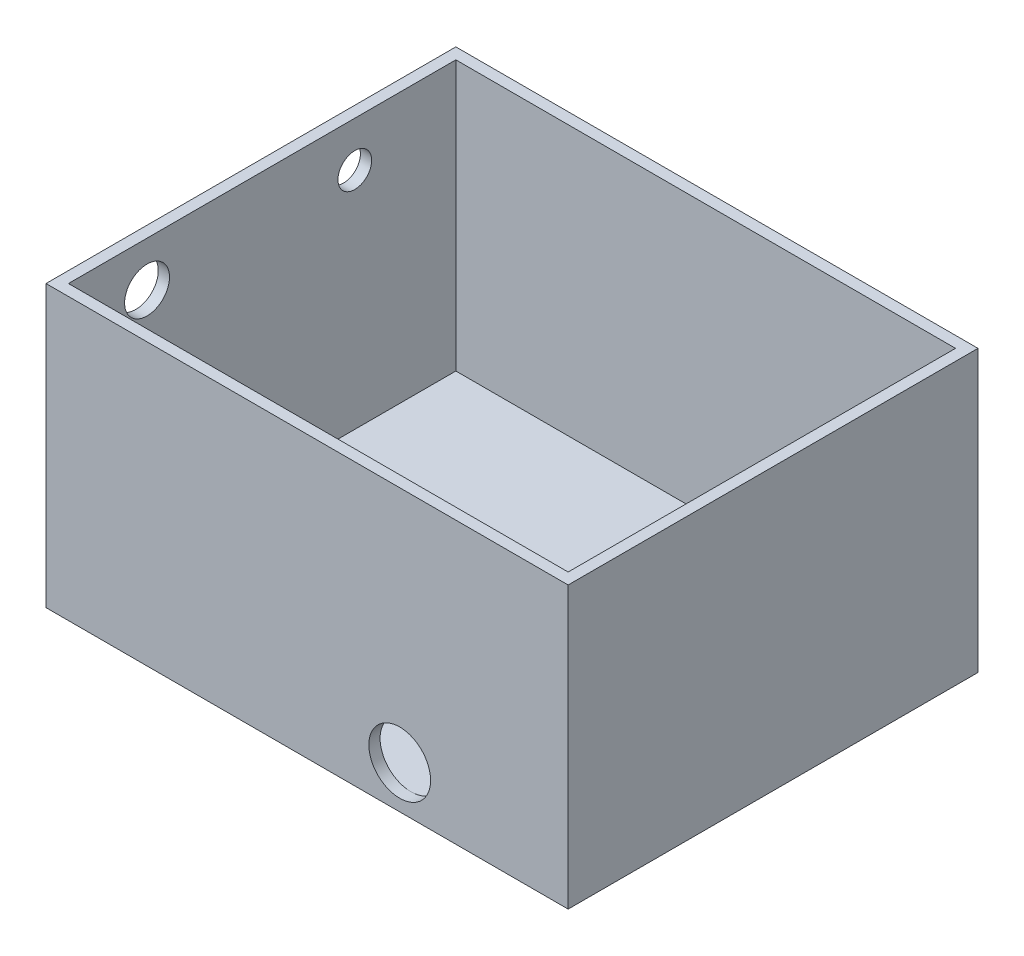
SolidWorks part; units mm, degrees
ref_plane "Front Plane" through (0, 0, 0) normal (0, 0, 1) x (1, 0, 0)
ref_plane "Top Plane" through (0, 0, 0) normal (0, 1, 0) x (1, 0, 0)
ref_plane "Right Plane" through (0, 0, 0) normal (1, 0, 0) x (0, 0, -1)
sketch "Sketch2" plane through (0, 0, 0) normal (0, 1, 0) x (1, 0, 0)
  line L1 (-59.055, 46.355) -> (59.055, 46.355)
  line L2 (-59.055, 46.355) -> (-59.055, -46.355)
  line L3 (-59.055, -46.355) -> (59.055, -46.355)
  line L4 (59.055, 46.355) -> (59.055, -46.355)
  line L5 (-59.055, 46.355) -> (59.055, -46.355) construction
  line L6 (-59.055, -46.355) -> (59.055, 46.355) construction
  point P0 (0, 0)
  dimension "D1" = 118.11
  dimension "D2" = 92.71
extrude "Boss-Extrude2" add sketch "Sketch2" along normal blind 63.5
shell "Shell1" thickness 2.54
sketch "Sketch3" plane through (0, 0, 46.355) normal (0, 0, 1) x (1, 0, 0)
  line L0 (59.055, 63.5) -> (59.055, 0) construction
  line L2 (-59.055, 0) -> (59.055, 0) construction
  circle A0 centre (20.955, 9.652) radius 6.985
  dimension "D1" = 13.97
  dimension "D2" = 38.1
  dimension "D3" = 9.652
extrude "Cut-Extrude1" cut sketch "Sketch3" against normal up to surface (90.17 mm away) up to face at (0, 33.02, -43.815)
sketch "Sketch4" plane through (-59.055, 0, 0) normal (-1, 0, 0) x (0, 0, 1)
  line L0 (-46.355, 0) -> (46.355, 0) construction
  line L1 (46.355, 63.5) -> (46.355, 0) construction
  circle A0 centre (26.035, 53.34) radius 5.08
  dimension "D3" = 10.16
  dimension "D1" = 53.34
  dimension "D2" = 20.32
extrude "Cut-Extrude2" cut sketch "Sketch4" against normal up to next
sketch "Sketch5" plane through (-59.055, 0, 0) normal (-1, 0, 0) x (0, 0, 1)
  line L1 (-46.355, 63.5) -> (-46.355, 0) construction
  line L2 (-46.355, 63.5) -> (46.355, 63.5) construction
  circle A0 centre (-20.955, 53.34) radius 3.81
  point P4 (0, 0)
  point P5 (0, 0)
  point P8 (0, 0)
  dimension "D1" = 7.62
  dimension "D2" = 25.4
  dimension "D3" = 10.16
extrude "Cut-Extrude3" cut sketch "Sketch5" against normal up to next
